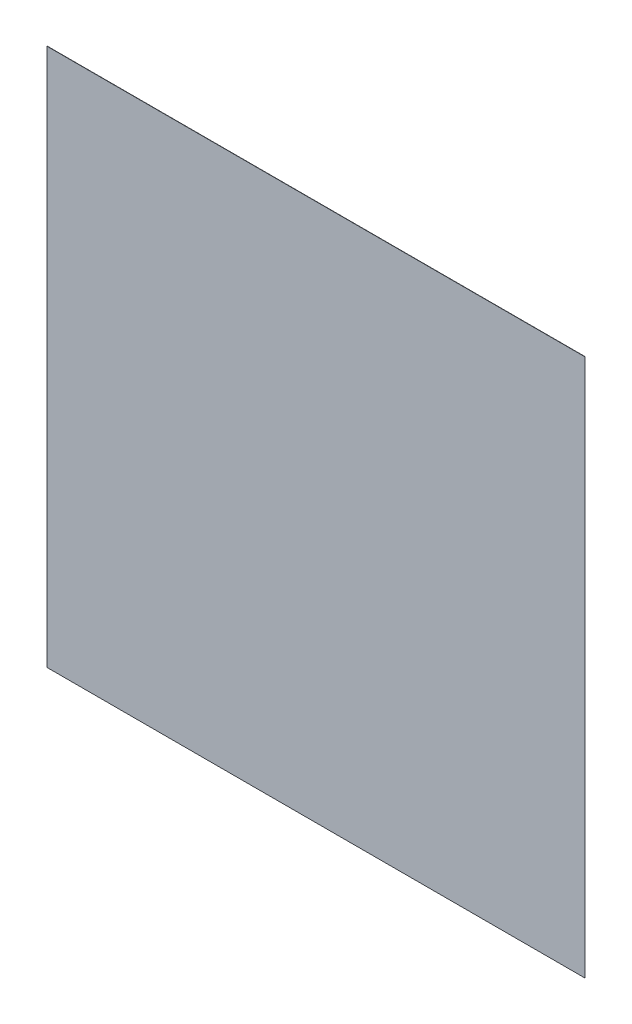
SolidWorks part; units mm, degrees
ref_plane "Plan de face" through (0, 0, 0) normal (0, 0, 1) x (1, 0, 0)
ref_plane "Plan de dessus" through (0, 0, 0) normal (0, 1, 0) x (1, 0, 0)
ref_plane "Plan de droite" through (0, 0, 0) normal (1, 0, 0) x (0, 0, -1)
sketch "Esquisse1" plane through (0, 0, 0) normal (0, 0, 1) x (1, 0, 0)
  line L1 (0, 1362.879) -> (2000, 1362.879)
  line L2 (0, 1362.879) -> (0, -637.121)
  line L3 (0, -637.121) -> (2000, -637.121)
  line L4 (2000, 1362.879) -> (2000, -637.121)
  dimension "D1" = 2000
  dimension "D2" = 2000
extrude "Boss.-Extru.1" add sketch "Esquisse1" along normal blind 1
